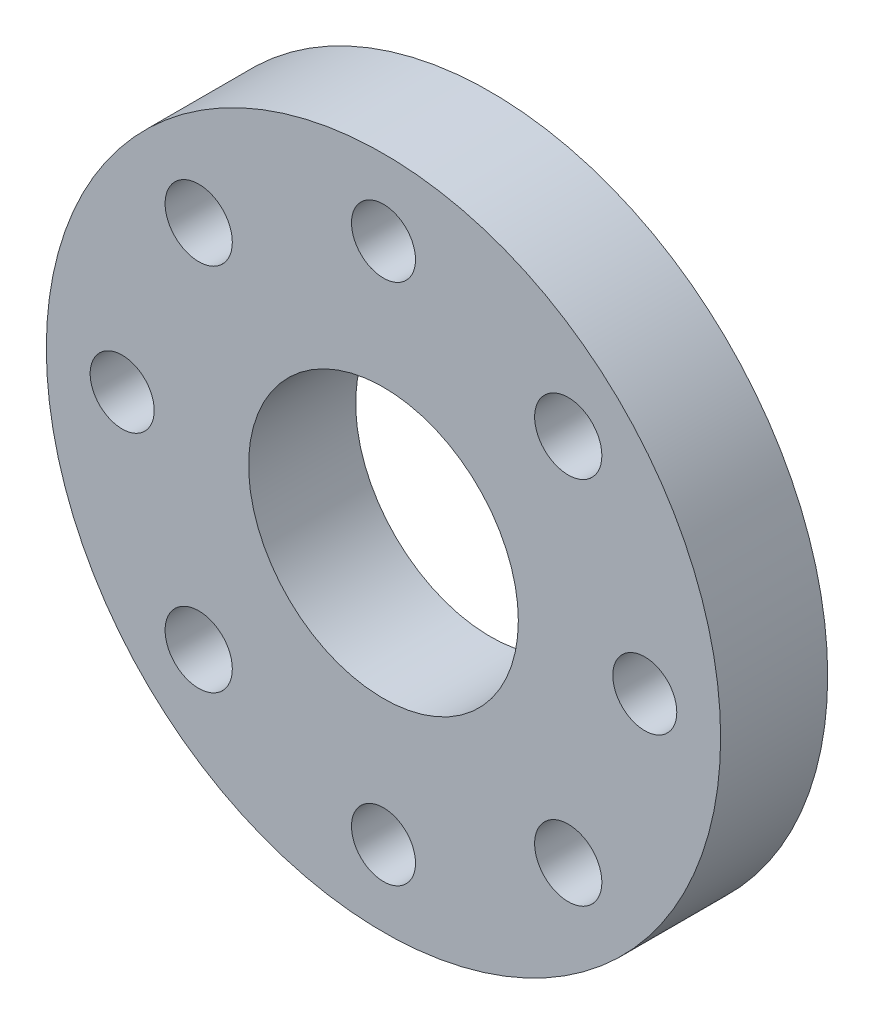
SolidWorks part; units mm, degrees
material "Balsa"
ref_plane "Front Plane" through (0, 0, 0) normal (0, 0, 1) x (1, 0, 0)
ref_plane "Top Plane" through (0, 0, 0) normal (0, 1, 0) x (1, 0, 0)
ref_plane "Right Plane" through (0, 0, 0) normal (1, 0, 0) x (0, 0, -1)
sketch "Sketch1" plane through (0, 0, 0) normal (0, 0, 1) x (1, 0, 0)
  circle A0 centre (0, 0) radius 20
  circle A8 centre (0, 0) radius 8
  circle A10 centre (0, 0) radius 15.5 construction
  circle A11 centre (0, -15.5) radius 1.8986
  circle A12 centre (10.9602, -10.9602) radius 1.9939
  circle A13 centre (-15.5, 0) radius 1.8986
  circle A14 centre (-10.9602, -10.9602) radius 1.9939
  circle A15 centre (0, 15.5) radius 1.8986
  circle A16 centre (-10.9602, 10.9602) radius 1.9939
  circle A17 centre (15.5, 0) radius 1.8986
  circle A18 centre (10.9602, 10.9602) radius 1.9939
  dimension "D4" = 16
  dimension "D9" = 3.7973
  dimension "D10" = 3.9878
  dimension "D5" = 31
  dimension "D2" = 40
  dimension "D11" = 45
  dimension "D12" = 4
extrude "Boss-Extrude1" add sketch "Sketch1" along normal blind 6.35
